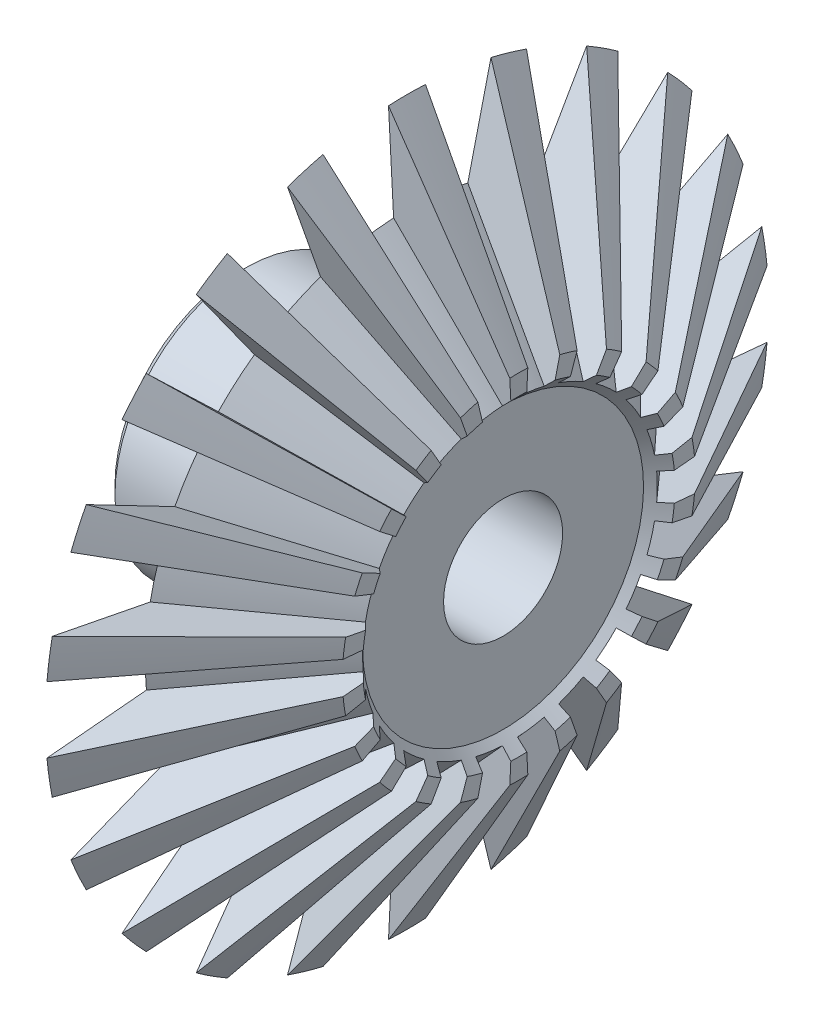
SolidWorks part; units mm, degrees
ref_plane "Plano frontal" through (0, 0, 0) normal (0, 0, 1) x (1, 0, 0)
ref_plane "Plano superior" through (0, 0, 0) normal (0, 1, 0) x (1, 0, 0)
ref_plane "Plano direito" through (0, 0, 0) normal (1, 0, 0) x (0, 0, -1)
sketch "Esboço1" plane through (0, 0, 0) normal (0, 0, 1) x (1, 0, 0)
  line L0 (0, 22.225) -> (104.7728, 22.225)
  line L1 (104.7728, 65.8844) -> (63.0254, 135)
  line L2 (63.0254, 135) -> (63.0254, 59.2125)
  line L3 (53.0254, 49.2125) -> (3.175, 49.2125)
  line L4 (3.175, 49.2125) -> (0, 46.0375)
  line L5 (0, 0) -> (104.7728, 0) construction
  line L7 (104.7728, 65.8844) -> (104.7728, 22.225)
  line L8 (0, 46.0375) -> (0, 22.225)
  arc A0 (63.0254, 59.2125) -> (53.0254, 49.2125) centre (53.0254, 59.2125) cw
  point P13 (0, 49.2125)
  dimension "D8" = 10
  dimension "D1" = 44.45
  dimension "D2" = 98.425
  dimension "D4" = 270
revolve "Revolução1" add sketch "Esboço1" angle 360 about L5
sketch "Esboço3" plane through (0, 0, 0) normal (0, 1, 0) x (1, 0, 0)
  line L0 (0, 0) -> (150.6955, 0) construction
  line L1 (63.0254, 135) -> (150.6955, 0) construction
  line L2 (104.7728, -65.8844) -> (104.7728, 65.8844) construction
  line L3 (104.7728, 51.347) -> (63.0254, 97.7122)
  line L4 (63.0254, 135) -> (63.0254, -135) construction
  line L5 (63.0254, 135) -> (63.0254, 97.7122)
  line L7 (111.5275, 60.3133) -> (104.7728, 51.347)
  line L9 (63.0254, 135) -> (111.5275, 60.3133)
  dimension "D1" = 48
  dimension "D2" = 57
revolve "Corte-Revolução2" cut sketch "Esboço3" angle 10.5 mid plane about L0
pattern_circular "PadrãoCircular1" count 22 over 360 about axis through (0, 0, 0) along (1, 0, 0) of "Corte-Revolução2"
sketch "Esboço2" plane through (0, 0, 0) normal (0, 0, 1) x (1, 0, 0)
  line L0 (104.9056, 58.4498) -> (98.9056, 52.4498)
  line L1 (98.9056, 52.4498) -> (98.9056, 18.9014)
  line L2 (98.9056, 18.9014) -> (104.9056, 18.9014)
  line L4 (104.9056, 18.9014) -> (104.9056, 58.4498)
  dimension "D1" = 45
  dimension "D3" = 6
revolve "Corte-Revolução1" cut sketch "Esboço2" angle 360 about axis through (104.7728, 0, 0) along (-1, 0, 0)
